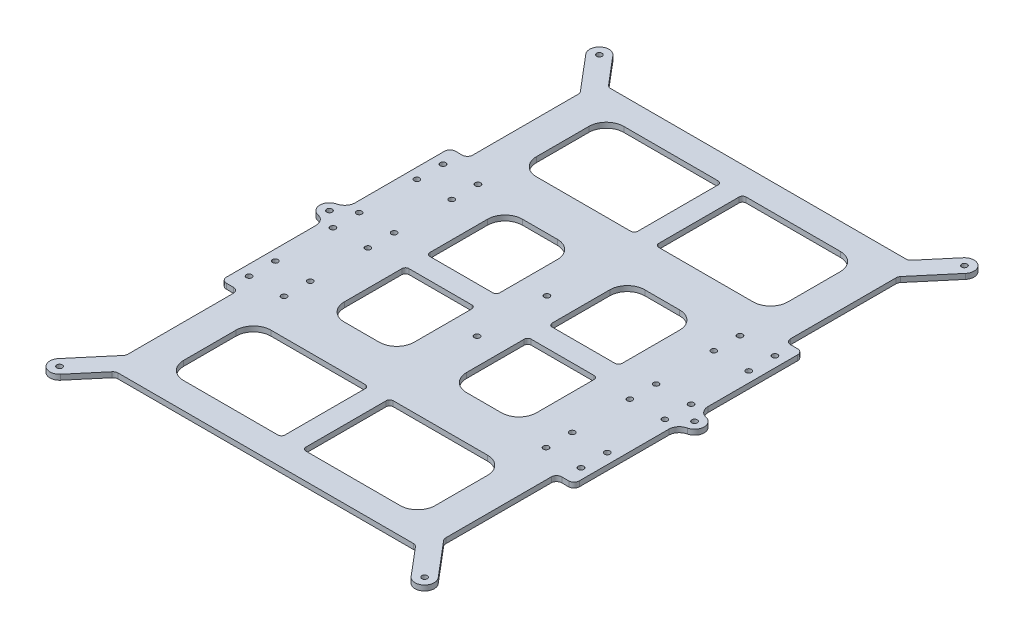
SolidWorks part; units mm, degrees
ref_plane "Alzado" through (0, 0, 0) normal (0, 0, 1) x (1, 0, 0)
ref_plane "Planta" through (0, 0, 0) normal (0, 1, 0) x (1, 0, 0)
ref_plane "Vista lateral" through (0, 0, 0) normal (1, 0, 0) x (0, 0, -1)
sketch "Croquis1" plane through (0, 0, 0) normal (0, 1, 0) x (1, 0, 0)
  line L0 (110, 320) -> (110, 0) construction
  line L1 (0, 0) -> (220, 0)
  line L2 (0, 0) -> (0, 320)
  line L3 (0, 320) -> (220, 320)
  line L4 (220, 0) -> (220, 320)
  line L5 (0, 160) -> (220, 160) construction
  line L6 (19, 320) -> (19, 0) construction
  line L7 (31, 320) -> (31, 0) construction
  line L8 (189, 320) -> (189, 0) construction
  line L9 (201, 320) -> (201, 0) construction
  line L10 (195, 320) -> (195, 0) construction
  line L11 (25, 320) -> (25, 0) construction
  line L12 (5.5, 314.5) -> (5.5, 160) construction
  circle A0 centre (185, 167.5) radius 1.55
  circle A1 centre (205, 167.5) radius 1.55
  circle A4 centre (185, 152.5) radius 1.55
  circle A5 centre (205, 152.5) radius 1.55
  circle A7 centre (35, 215.5) radius 1.575
  circle A8 centre (35, 200.5) radius 1.575
  circle A10 centre (35, 119.5) radius 1.575
  circle A13 centre (35, 104.5) radius 1.575
  circle A14 centre (5.5, 314.5) radius 1.575
  circle A15 centre (214.5, 314.5) radius 1.575
  circle A16 centre (214.5, 5.5) radius 1.575
  circle A17 centre (5.5, 5.5) radius 1.575
  circle A18 centre (15, 200.5) radius 1.575
  circle A19 centre (15, 215.5) radius 1.575
  circle A20 centre (15, 104.5) radius 1.575
  circle A21 centre (15, 119.5) radius 1.575
  circle A22 centre (110, 180) radius 1.575
  circle A23 centre (110, 140) radius 1.575
  circle A24 centre (185, 104.5) radius 1.575
  circle A25 centre (205, 104.5) radius 1.575
  circle A26 centre (205, 119.5) radius 1.575
  circle A27 centre (185, 119.5) radius 1.575
  circle A28 centre (185, 200.5) radius 1.575
  circle A29 centre (185, 215.5) radius 1.575
  circle A30 centre (205, 200.5) radius 1.575
  circle A31 centre (205, 215.5) radius 1.575
  circle A32 centre (5.5, 160) radius 1.575
  circle A33 centre (35, 152.5) radius 1.55
  circle A34 centre (15, 152.5) radius 1.55
  circle A35 centre (15, 167.5) radius 1.55
  circle A36 centre (35, 167.5) radius 1.55
  circle A37 centre (214.5, 160) radius 1.575
  dimension "D8" = 3.1
  dimension "D13" = 6
  dimension "D14" = 3.15
  dimension "D17" = 3.15
  dimension "D23" = 3.15
  dimension "D18" = 20
  dimension "D1" = 320
  dimension "D2" = 220
  dimension "D3" = 12
  dimension "D4" = 12
  dimension "D5" = 158
  dimension "D6" = 19
  dimension "D7" = 6
  dimension "D9" = 20
  dimension "D10" = 10
  dimension "D11" = 7.5
  dimension "D12" = 7.5
  dimension "D15" = 10
  dimension "D16" = 15
  dimension "D20" = 10
  dimension "D21" = 104.5
  dimension "D24" = 5.5
  dimension "D25" = 5.5
extrude "Saliente-Extruir1" add sketch "Croquis1" along normal blind 3
sketch "Croquis2" plane through (0, 3, 0) normal (0, 1, 0) x (1, 0, 0)
  line L0 (220, 160) -> (0, 160) construction
  line L2 (9, 9) -> (211, 9) construction
  line L3 (220, 0) -> (220, 320) construction
  line L4 (9, 148.775) -> (9, 94.5)
  line L5 (110, 320) -> (110, 0) construction
  line L6 (220, 320) -> (0, 320) construction
  line L7 (0, 0) -> (220, 0) construction
  line L8 (9, 9) -> (211, 9)
  line L9 (211, 9) -> (211, 311)
  line L10 (211, 311) -> (9, 311)
  line L11 (9, 311) -> (9, 9)
  line L15 (9, 225.5) -> (9, 171.225)
  line L16 (9, 225.5) -> (19, 225.5)
  line L18 (19, 94.5) -> (9, 94.5)
  line L19 (19, 94.5) -> (19, 30)
  line L20 (24.1066, 19) -> (195.8934, 19)
  line L21 (210.2988, 1.9504) -> (195.8934, 19)
  line L22 (1.2988, 9.0496) -> (19, 30)
  line L23 (9.7012, 1.9504) -> (24.1066, 19)
  line L24 (9, 148.775) -> (9, 9) construction
  line L25 (19, 148.775) -> (19, 19) construction
  line L26 (19, 19) -> (201, 19) construction
  line L27 (211, 9) -> (211, 311) construction
  line L28 (19, 225.5) -> (19, 290)
  line L29 (24.1066, 301) -> (195.8934, 301)
  line L30 (1.2988, 310.9504) -> (19, 290)
  line L31 (9.7012, 318.0496) -> (24.1066, 301)
  line L32 (0, 320) -> (0, 0) construction
  line L33 (218.7012, 9.0496) -> (201, 30)
  line L34 (201, 19) -> (201, 311) construction
  line L35 (201, 94.5) -> (201, 30)
  line L36 (201, 94.5) -> (211, 94.5)
  line L37 (211, 148.775) -> (211, 94.5)
  line L38 (211, 225.5) -> (211, 171.225)
  line L39 (211, 225.5) -> (201, 225.5)
  line L40 (201, 225.5) -> (201, 290)
  line L41 (218.7012, 310.9504) -> (201, 290)
  line L42 (210.2988, 318.0496) -> (195.8934, 301)
  line L43 (182, 276) -> (182, 246)
  line L44 (102, 286) -> (48, 286)
  line L46 (102, 236) -> (48, 236)
  line L47 (38, 276) -> (38, 246)
  line L48 (118, 236) -> (172, 236)
  line L52 (104, 284) -> (104, 238)
  line L53 (116, 284) -> (116, 238)
  line L54 (118, 286) -> (172, 286)
  line L55 (102, 84) -> (48, 84)
  line L56 (38, 44) -> (38, 74)
  line L57 (102, 34) -> (48, 34)
  line L58 (104, 36) -> (104, 82)
  line L59 (116, 36) -> (116, 82)
  line L60 (118, 34) -> (172, 34)
  line L61 (182, 44) -> (182, 74)
  line L62 (118, 84) -> (172, 84)
  line L63 (55, 152) -> (55, 119)
  line L64 (93, 166) -> (57, 166)
  line L65 (95, 168) -> (95, 201)
  line L66 (85, 211) -> (65, 211)
  line L67 (55, 168) -> (55, 201)
  line L68 (85, 109) -> (65, 109)
  line L69 (95, 152) -> (95, 119)
  line L70 (93, 154) -> (57, 154)
  line L71 (135, 109) -> (155, 109)
  line L72 (165, 152) -> (165, 119)
  line L73 (125, 152) -> (125, 119)
  line L74 (127, 154) -> (163, 154)
  line L75 (127, 166) -> (163, 166)
  line L76 (165, 168) -> (165, 201)
  line L77 (135, 211) -> (155, 211)
  line L78 (125, 168) -> (125, 201)
  arc A2 (1.2988, 9.0496) -> (9.7012, 1.9504) centre (5.5, 5.5) ccw
  arc A3 (4.3043, 165.3685) -> (4.3043, 154.6315) centre (5.5, 160) ccw
  arc A4 (9, 148.775) -> (4.3043, 154.6315) centre (3, 148.775) ccw
  arc A5 (9, 171.225) -> (4.3043, 165.3685) centre (3, 171.225) cw
  circle A6 centre (35, 215.5) radius 1.575 construction
  circle A7 centre (35, 104.5) radius 1.575 construction
  arc A8 (48, 236) -> (38, 246) centre (48, 246) cw
  arc A10 (1.2988, 310.9504) -> (9.7012, 318.0496) centre (5.5, 314.5) cw
  arc A11 (218.7012, 9.0496) -> (210.2988, 1.9504) centre (214.5, 5.5) cw
  arc A12 (211, 148.775) -> (215.6957, 154.6315) centre (217, 148.775) cw
  arc A13 (215.6957, 165.3685) -> (215.6957, 154.6315) centre (214.5, 160) cw
  arc A14 (211, 171.225) -> (215.6957, 165.3685) centre (217, 171.225) ccw
  arc A15 (218.7012, 310.9504) -> (210.2988, 318.0496) centre (214.5, 314.5) ccw
  arc A16 (48, 286) -> (38, 276) centre (48, 276) ccw
  arc A17 (172, 236) -> (182, 246) centre (172, 246) ccw
  arc A18 (172, 286) -> (182, 276) centre (172, 276) cw
  arc A19 (48, 84) -> (38, 74) centre (48, 74) ccw
  arc A20 (48, 34) -> (38, 44) centre (48, 44) cw
  arc A21 (172, 34) -> (182, 44) centre (172, 44) ccw
  arc A22 (172, 84) -> (182, 74) centre (172, 74) cw
  arc A23 (102, 236) -> (104, 238) centre (102, 238) ccw
  arc A24 (102, 286) -> (104, 284) centre (102, 284) cw
  arc A25 (116, 284) -> (118, 286) centre (118, 284) cw
  arc A26 (118, 236) -> (116, 238) centre (118, 238) cw
  arc A27 (116, 82) -> (118, 84) centre (118, 82) cw
  arc A28 (116, 36) -> (118, 34) centre (118, 36) ccw
  arc A29 (102, 34) -> (104, 36) centre (102, 36) ccw
  arc A30 (102, 84) -> (104, 82) centre (102, 82) cw
  arc A31 (95, 201) -> (85, 211) centre (85, 201) ccw
  arc A32 (65, 211) -> (55, 201) centre (65, 201) ccw
  arc A33 (65, 109) -> (55, 119) centre (65, 119) cw
  arc A34 (95, 119) -> (85, 109) centre (85, 119) cw
  arc A35 (155, 109) -> (165, 119) centre (155, 119) ccw
  arc A36 (125, 119) -> (135, 109) centre (135, 119) ccw
  arc A37 (155, 211) -> (165, 201) centre (155, 201) cw
  arc A38 (125, 201) -> (135, 211) centre (135, 201) cw
  arc A39 (127, 166) -> (125, 168) centre (127, 168) cw
  arc A40 (163, 166) -> (165, 168) centre (163, 168) ccw
  arc A41 (165, 152) -> (163, 154) centre (163, 152) ccw
  arc A42 (125, 152) -> (127, 154) centre (127, 152) cw
  arc A43 (55, 152) -> (57, 154) centre (57, 152) cw
  arc A44 (95, 152) -> (93, 154) centre (93, 152) ccw
  arc A45 (93, 166) -> (95, 168) centre (93, 168) ccw
  arc A46 (57, 166) -> (55, 168) centre (57, 168) cw
  point P28 (110, 19)
  point P71 (110, 301)
  point P76 (38, 236)
  point P79 (38, 286)
  point P106 (104, 236)
  point P109 (104, 286)
  point P112 (116, 286)
  point P115 (116, 236)
  point P118 (116, 84)
  point P121 (116, 34)
  point P124 (104, 34)
  point P127 (104, 84)
  point P137 (95, 211)
  point P140 (55, 211)
  point P167 (125, 166)
  point P170 (165, 166)
  point P173 (165, 154)
  point P176 (125, 154)
  point P179 (55, 154)
  point P182 (95, 154)
  point P185 (95, 166)
  point P188 (55, 166)
  dimension "D2" = 11
  dimension "D3" = 11
  dimension "D4" = 6
  dimension "D5" = 10
  dimension "D6" = 10
  dimension "D7" = 50
  dimension "D12" = 10
  dimension "D14" = 2
  dimension "D19" = 10
  dimension "D20" = 2
  dimension "D9" = 30
  dimension "D10" = 15
  dimension "D8" = 19
  dimension "D11" = 38
  dimension "D13" = 6
  dimension "D15" = 6
  dimension "D16" = 15
  dimension "D17" = 40
  dimension "D18" = 45
  dimension "D1" = 9
extrude "Cortar-Extruir1" cut sketch "Croquis2" against normal up to surface (3 mm away) flip side to cut up to face at (35, 0, -169.05)
fillet "Redondeo1" radius 3 16 edges at (211, 1.5, -225.5) (211, 1.5, -94.5) (9, 1.5, -225.5) (9, 1.5, -94.5) (24.1066, 1.5, -301) (195.8934, 1.5, -301) (201, 1.5, -290) (201, 1.5, -225.5) (201, 1.5, -94.5) (201, 1.5, -30) (195.8934, 1.5, -19) (24.1066, 1.5, -19) (19, 1.5, -30) (19, 1.5, -94.5) (19, 1.5, -290) (19, 1.5, -225.5)
